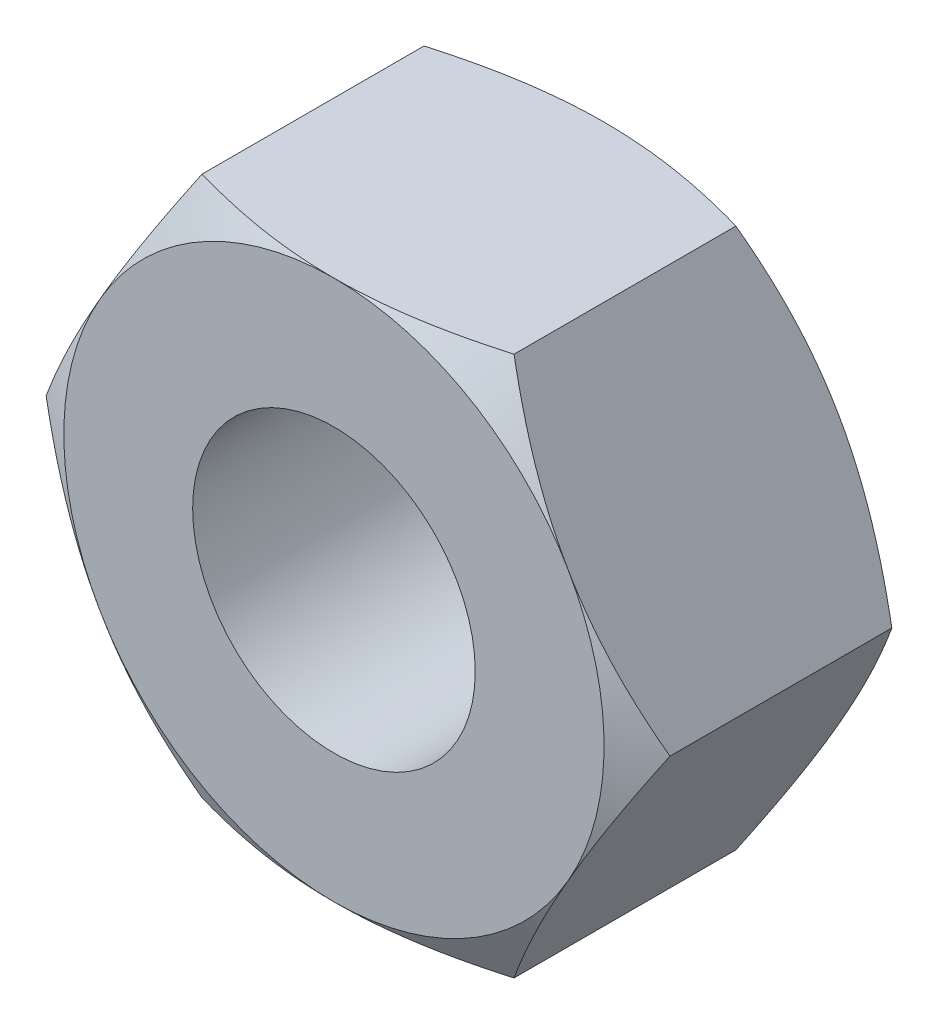
SolidWorks part; units mm, degrees
ref_plane "Front Plane" through (0, 0, 0) normal (0, 0, 1) x (1, 0, 0)
ref_plane "Top Plane" through (0, 0, 0) normal (0, 1, 0) x (1, 0, 0)
ref_plane "Right Plane" through (0, 0, 0) normal (1, 0, 0) x (0, 0, -1)
sketch "Sketch1" plane through (0, 0, 0) normal (0, 0, 1) x (1, 0, 0)
  line L1 (3.7528, -6.5) -> (7.5056, 0)
  line L2 (7.5056, 0) -> (3.7528, 6.5)
  line L3 (3.7528, 6.5) -> (-3.7528, 6.5)
  line L4 (-3.7528, 6.5) -> (-7.5056, 0)
  line L5 (-7.5056, 0) -> (-3.7528, -6.5)
  line L6 (-3.7528, -6.5) -> (3.7528, -6.5)
  circle A0 centre (0, 0) radius 6.5 construction
  dimension "D1" = 13
extrude "Boss-Extrude1" add sketch "Sketch1" along normal blind 6.5
sketch "Sketch3" plane through (0, 0, 0) normal (1, 0, 0) x (0, 0, -1)
  line L0 (0, 0) -> (17.6373, 0) construction
  line L1 (-1.7116, 9.4646) -> (0, 6.5)
  line L3 (0, 6.5) -> (0, 9.4646)
  line L4 (0, 9.4646) -> (-1.7116, 9.4646)
  line L7 (-6.5, 6.5) -> (-6.5, 9.3766)
  line L8 (-6.5, 9.3766) -> (-4.8392, 9.3766)
  line L10 (-6.5, 6.5) -> (-4.8392, 9.3766)
  dimension "D1" = 30
  dimension "D2" = 30
revolve "Cut-Revolve1" cut sketch "Sketch3" angle 360 about L0
hole_wizard "M8 Tapped Hole1" positions "3DSketch1" profile "Sketch4" tap size "M8" standard "ISO" end condition through all
sketch3d "3DSketch1"
  point P0 (0, 0, 6.5)
sketch "Sketch4" plane through (0, 0, 6.5) normal (1, 0, 0) x (0, -1, 0)
  line L0 (0, 0) -> (0, 6.5)
  line L1 (0, 6.5) -> (3.4, 6.5)
  line L2 (3.4, 6.5) -> (3.4, 0)
  line L5 (3.4, 0) -> (0, 0)
  line L11 (0, -6.35) -> (0, 107.95) construction
  dimension "Thru Tap Drill Dia." = 6.8
  dimension "Thru Tap Drill Depth" = 6.5
cosmetic thread "Hole Thread1" parameters "D2"=8
